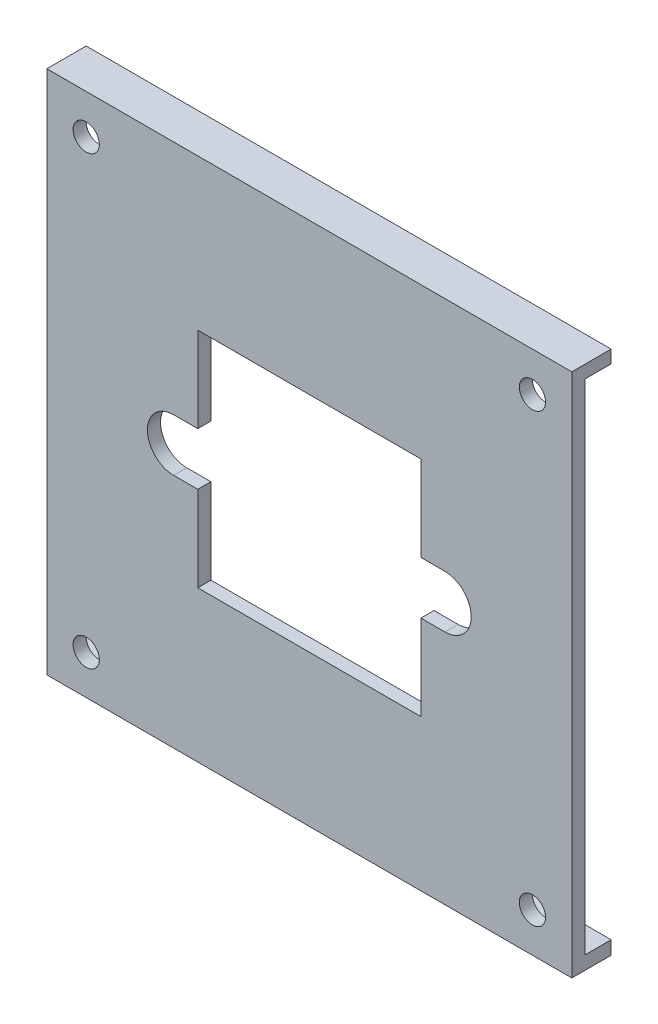
SolidWorks part; units mm, degrees
ref_plane "Front Plane" through (0, 0, 0) normal (0, 0, 1) x (1, 0, 0)
ref_plane "Top Plane" through (0, 0, 0) normal (0, 1, 0) x (1, 0, 0)
ref_plane "Right Plane" through (0, 0, 0) normal (1, 0, 0) x (0, 0, -1)
sketch "Sketch1" plane through (0, 0, 0) normal (0, 0, 1) x (1, 0, 0)
  line L0 (0, 0) -> (0, 40)
  line L1 (0, 40) -> (40, 40)
  line L2 (40, 40) -> (40, 0)
  line L3 (40, 0) -> (0, 0)
  dimension "D1" = 40
  dimension "D2" = 40
extrude "Boss-Extrude1" add sketch "Sketch1" along normal blind 3
sketch "Sketch2" plane through (0, 0, 3) normal (0, 0, 1) x (1, 0, 0)
  line L0 (40, 40) -> (0, 40) construction
  line L1 (0, 40) -> (0, 0) construction
  line L2 (0, 0) -> (40, 0) construction
  line L3 (40, 0) -> (40, 40) construction
  circle A0 centre (3, 37) radius 1
  circle A1 centre (3, 3) radius 1
  circle A2 centre (37, 37) radius 1
  circle A3 centre (37, 3) radius 1
  dimension "D1" = 2
  dimension "D4" = 2
  dimension "D7" = 2
  dimension "D10" = 2
  dimension "D2" = 3
  dimension "D3" = 3
  dimension "D5" = 3
  dimension "D6" = 3
  dimension "D8" = 3
  dimension "D9" = 3
  dimension "D11" = 3
  dimension "D12" = 3
extrude "Cut-Extrude1" cut sketch "Sketch2" against normal blind 10
sketch "Sketch3" plane through (0, 0, 0) normal (0, 0, -1) x (-1, 0, 0)
  line L0 (-40, 40) -> (0, 40) construction
  line L1 (-28.5, 28.5) -> (-11.5, 28.5)
  line L2 (-28.5, 28.5) -> (-28.5, 11.5)
  line L3 (-28.5, 11.5) -> (-11.5, 11.5)
  line L4 (-11.5, 28.5) -> (-11.5, 11.5)
  line L5 (0, 40) -> (0, 0) construction
  dimension "D1" = 17
  dimension "D2" = 17
  dimension "D3" = 11.5
  dimension "D4" = 11.5
extrude "Cut-Extrude3" cut sketch "Sketch3" against normal blind 10
sketch "Sketch4" plane through (40, 0, 0) normal (1, 0, 0) x (0, 0, -1)
  line L0 (0, 39.0249) -> (-2, 39.0249)
  line L1 (0, 0) -> (0, 40) construction
  line L2 (-2, 39.0249) -> (-2, 1.0249)
  line L3 (-2, 1.0249) -> (0, 1.0249)
  line L4 (0, 1.0249) -> (0, 39.0249)
  dimension "D1" = 2
  dimension "D2" = 38
extrude "Cut-Extrude4" cut sketch "Sketch4" against normal through all
sketch "Sketch6" plane through (0, 0, 3) normal (0, 0, 1) x (1, 0, 0)
  line L0 (9, 20) -> (31, 20) construction
  line L7 (11.5, 11.5) -> (11.5, 28.5) construction
  line L9 (11.5, 28.5) -> (28.5, 28.5) construction
  dimension "D1" = 22
  dimension "D2" = 2.5
  dimension "D3" = 8.5
sketch "Sketch7" plane through (0, 0, 3) normal (0, 0, 1) x (1, 0, 0)
  line L0 (11.5, 22) -> (9.6649, 22)
  line L2 (11.5, 11.5) -> (11.5, 28.5) construction
  line L3 (11.5, 18) -> (9.6649, 18)
  line L4 (9, 20) -> (31, 20) construction
  line L5 (11.5, 22) -> (11.5, 18)
  line L6 (20, 40) -> (20, 0) construction
  line L7 (40, 40) -> (0, 40) construction
  line L8 (0, 0) -> (40, 0) construction
  line L9 (28.5, 22) -> (30.3351, 22)
  line L10 (28.5, 18) -> (30.3351, 18)
  line L11 (28.5, 22) -> (28.5, 18)
  arc A0 (9.6649, 22) -> (9.6649, 18) centre (9.6649, 20) ccw
  arc A1 (30.3351, 22) -> (30.3351, 18) centre (30.3351, 20) cw
  dimension "D1" = 2
  dimension "D2" = 2
extrude "Cut-Extrude5" cut sketch "Sketch7" against normal through all
sketch "Sketch8" plane through (0, 0, 3) normal (0, 0, 1) x (1, 0, 0)
  line L0 (20, 40) -> (20, 0) construction
  line L1 (40, 40) -> (0, 40) construction
  line L2 (0, 0) -> (40, 0) construction
